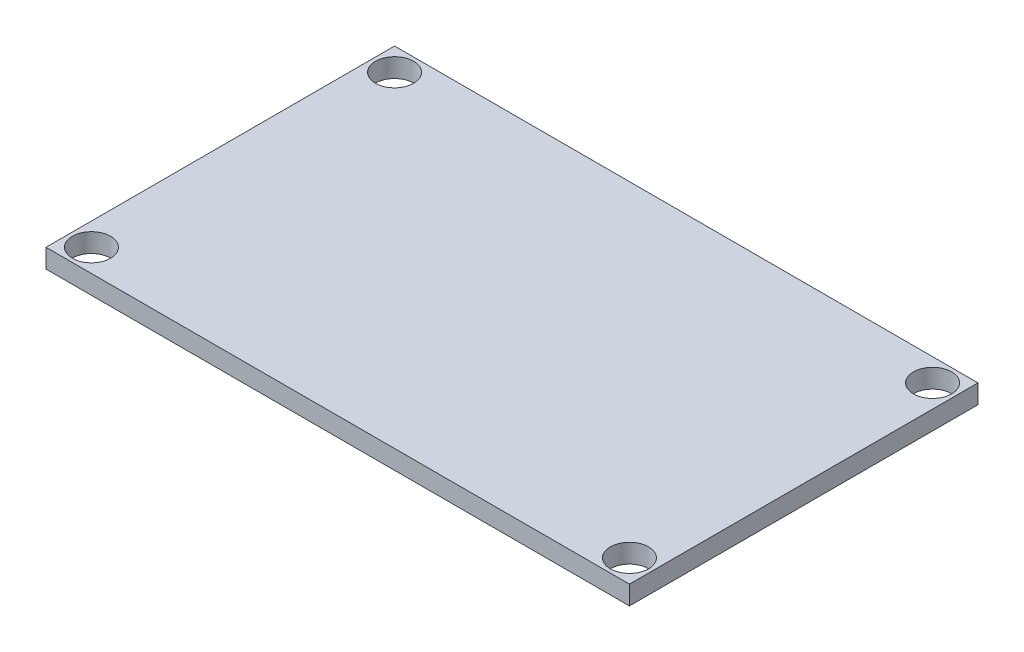
SolidWorks part; units mm, degrees
material "6061-T6 (SS)"
ref_plane "Front Plane" through (0, 0, 0) normal (0, 0, 1) x (1, 0, 0)
ref_plane "Top Plane" through (0, 0, 0) normal (0, 1, 0) x (1, 0, 0)
ref_plane "Right Plane" through (0, 0, 0) normal (1, 0, 0) x (0, 0, -1)
sketch "Sketch1" plane through (0, 0, 0) normal (0, 1, 0) x (1, 0, 0)
  line L1 (-24.4475, 14.605) -> (24.4475, 14.605)
  line L2 (-24.4475, 14.605) -> (-24.4475, -14.605)
  line L3 (-24.4475, -14.605) -> (24.4475, -14.605)
  line L4 (24.4475, 14.605) -> (24.4475, -14.605)
  line L5 (-24.4475, 14.605) -> (24.4475, -14.605) construction
  line L6 (-24.4475, -14.605) -> (24.4475, 14.605) construction
  circle A0 centre (-22.5425, 12.7) radius 1.6
  circle A1 centre (-22.5425, -12.7) radius 1.6
  circle A2 centre (22.5425, -12.7) radius 1.6
  circle A3 centre (22.5425, 12.7) radius 1.6
  point P0 (0, 0)
  point P14 (0, 0)
  point P15 (0, 0)
  point P16 (0, 0)
  point P17 (0, 0)
  dimension "D5" = 3.2
  dimension "D1" = 29.21
  dimension "D2" = 48.895
  dimension "D3" = 1.905
  dimension "D4" = 1.905
  dimension "D6" = 1.905
  dimension "D7" = 1.905
extrude "Boss-Extrude1" add sketch "Sketch1" along normal blind 1.5875
